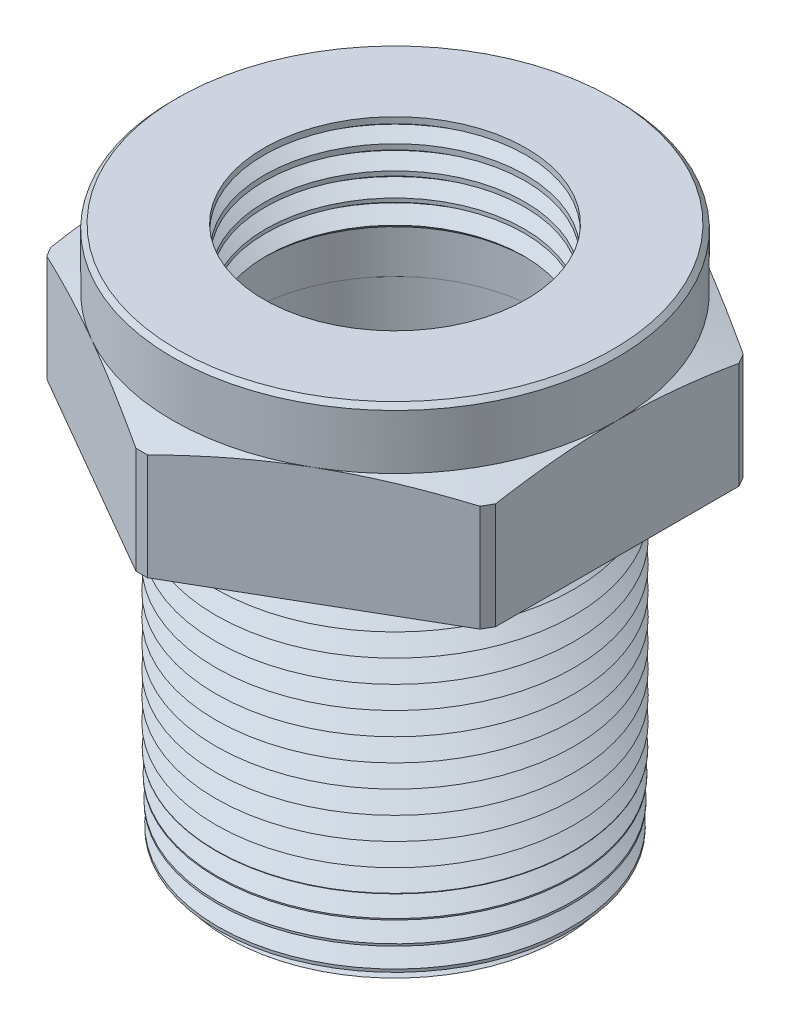
SolidWorks part; units mm, degrees
ref_plane "Front Plane" through (0, 0, 0) normal (0, 0, 1) x (1, 0, 0)
ref_plane "Top Plane" through (0, 0, 0) normal (0, 1, 0) x (1, 0, 0)
ref_plane "Right Plane" through (0, 0, 0) normal (1, 0, 0) x (0, 0, -1)
sketch "Sketch1" plane through (0, 0, 0) normal (0, 0, 1) x (1, 0, 0)
  line L0 (0, 0) -> (0, 68.999) construction
  line L1 (8.3312, 0) -> (9.8886, 0)
  line L2 (9.8886, 0) -> (10.414, 20.066)
  line L3 (10.414, 20.066) -> (14.1884, 20.066)
  line L4 (14.1884, 20.066) -> (14.1884, 26.6598)
  line L5 (14.1884, 26.6598) -> (12.446, 26.6598)
  line L6 (12.446, 26.6598) -> (12.446, 29.972)
  line L7 (12.446, 29.972) -> (7.3426, 29.972)
  line L8 (7.2009, 24.5618) -> (7.3426, 29.972)
  line L9 (7.2009, 24.5618) -> (8.281, 24.5618)
  line L10 (8.281, 24.5618) -> (8.281, 21.5646)
  line L11 (8.281, 21.5646) -> (8.3312, 21.5646)
  line L12 (8.3312, 21.5646) -> (8.3312, 0)
  dimension "D1" = 1.5
  dimension "D2" = 1.5
  dimension "A" = 20.828
  dimension "0.8A" = 16.6624
  dimension "B" = 14.4018
  dimension "T" = 20.066
  dimension "H" = 29.972
  dimension "0.22H" = 6.5938
  dimension "W1" = 28.3769
  dimension "1.1B" = 16.5621
  dimension "T+.05H" = 21.5646
  dimension "W" = 24.892
  dimension ".1H" = 2.9972
revolve "Revolve1" add sketch "Sketch1" angle 360 about L0
sketch "Sketch2" plane through (0, 20.066, 0) normal (0, -1, 0) x (1, 0, 0)
  line L1 (12.446, 7.1857) -> (0, 14.3714)
  line L2 (0, 14.3714) -> (-12.446, 7.1857)
  line L3 (-12.446, 7.1857) -> (-12.446, -7.1857)
  line L4 (-12.446, -7.1857) -> (0, -14.3714)
  line L5 (0, -14.3714) -> (12.446, -7.1857)
  line L6 (12.446, -7.1857) -> (12.446, 7.1857)
  circle A0 centre (0, 0) radius 12.446 construction
  dimension "Wr" = 24.892
extrude "Cut-Extrude1" cut sketch "Sketch2" against normal through all flip side to cut
sketch "Sketch4" plane through (0, 26.6598, 0) normal (0, 1, 0) x (-1, 0, 0)
  circle A0 centre (0, 0) radius 12.446 construction
  circle A1 centre (0, 0) radius 12.446
extrude "Cut-Extrude3" cut sketch "Sketch4" against normal blind 1.27 draft 70 flip side to cut
chamfer "Chamfer2" distance 0.254 angle 45 1 edges at (0, 24.5618, -7.2009)
sketch "Sketch7" plane through (0, 0, 0) normal (0, 0, 1) x (1, 0, 0)
  line L0 (-7.2074, 24.8093) -> (-7.236, 25.9007)
  line L1 (-7.3426, 29.972) -> (-7.2074, 24.8093) construction
  line L2 (-7.236, 25.9007) -> (-8.001, 25.3346)
  line L3 (-8.001, 25.3346) -> (-7.2074, 24.8093)
  line L4 (0, 0) -> (0, 27.6835) construction
  dimension "D1" = 55
  dimension "D2" = 55
  dimension "D3" = 16.002
revolve "Cut-Revolve1" cut sketch "Sketch7" angle 360 about L4
pattern_linear "LPattern1" count 5 spacing 1.27 along (0, 1, 0) of "Cut-Revolve1"
sketch "Sketch8" plane through (0, 0, 0) normal (0, 0, 1) x (1, 0, 0)
  line L0 (-10.414, 20.066) -> (-9.1212, 19.2103)
  line L1 (-9.1212, 19.2103) -> (-10.3674, 18.2881)
  line L2 (-10.414, 20.066) -> (-9.8886, 0) construction
  line L3 (-10.3674, 18.2881) -> (-10.414, 20.066)
  line L5 (0, 0) -> (0, 25.4984) construction
  dimension "D1" = 55
  dimension "D2" = 55
  dimension "D3" = 1.27
revolve "Cut-Revolve2" cut sketch "Sketch8" angle 360 about L5
pattern_linear "LPattern2" count 16 spacing 1.27 along (0, -1, 0) of "Cut-Revolve2"
chamfer "Chamfer3" distance 0.254 angle 45 1 edges at (0, 29.972, -12.446)
